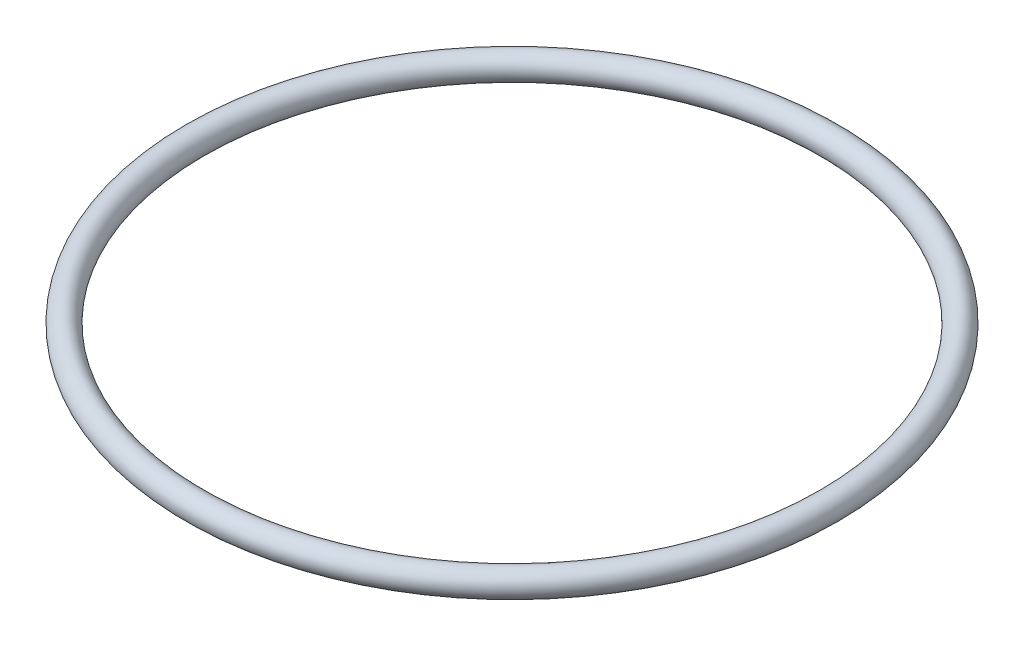
SolidWorks part; units mm, degrees
ref_plane "Front Plane" through (0, 0, 0) normal (0, 0, 1) x (1, 0, 0)
ref_plane "Top Plane" through (0, 0, 0) normal (0, 1, 0) x (1, 0, 0)
ref_plane "Right Plane" through (0, 0, 0) normal (1, 0, 0) x (0, 0, -1)
sketch "Sketch1" plane through (0, 0, 0) normal (0, 1, 0) x (1, 0, 0)
  circle A0 centre (0, 0) radius 32.3
  dimension "D1" = 64.6
sketch "Sketch2" plane through (0, 0, 0) normal (0, 0, 1) x (1, 0, 0)
  line L0 (32.3, 0) -> (-32.3, 0) construction
  circle A0 centre (-32.3, 0) radius 1.3
  dimension "D1" = 2.6
  dimension "D2" = 32.3
sweep "Sweep1" add profiles "Sketch2" path "Sketch1"
